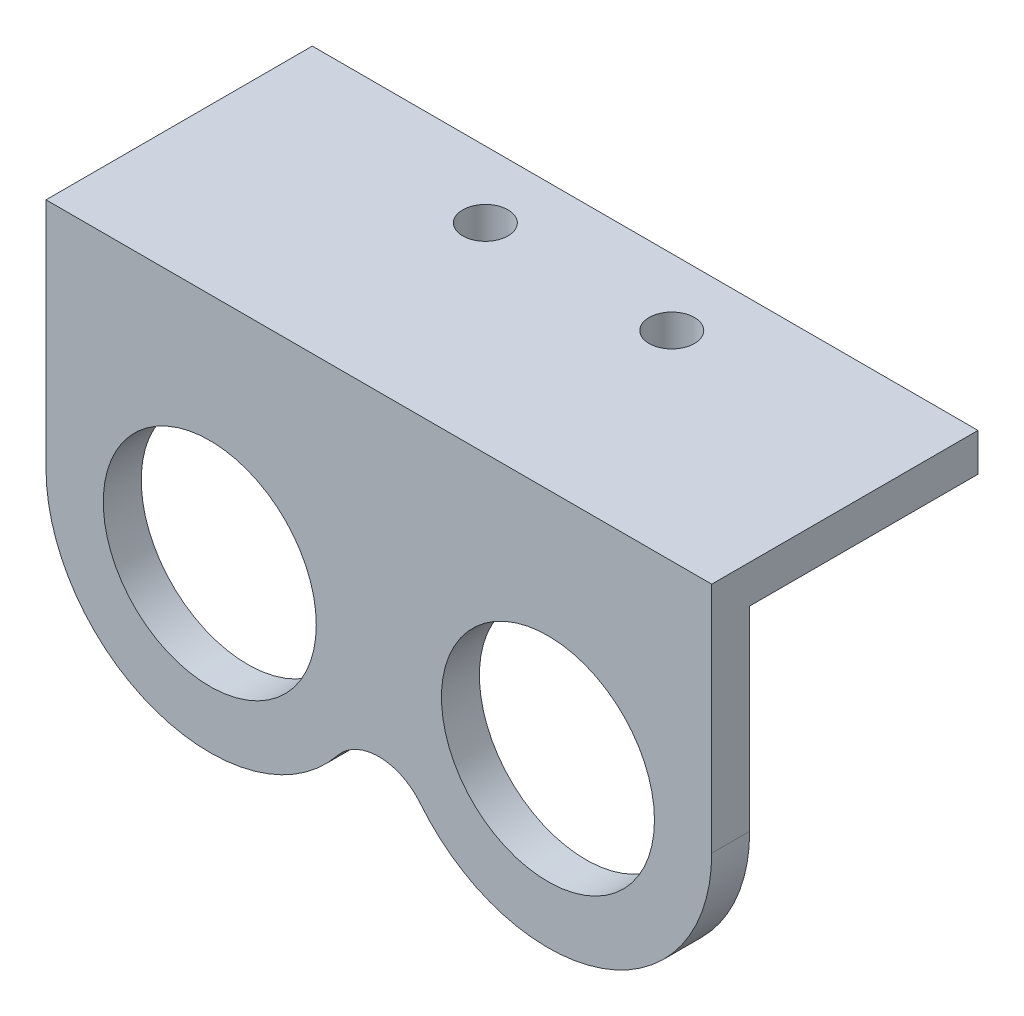
SolidWorks part; units mm, degrees
ref_plane "Front Plane" through (0, 0, 0) normal (0, 0, 1) x (1, 0, 0)
ref_plane "Top Plane" through (0, 0, 0) normal (0, 1, 0) x (1, 0, 0)
ref_plane "Right Plane" through (0, 0, 0) normal (1, 0, 0) x (0, 0, -1)
sketch "Sketch2" plane through (0, 0, 0) normal (0, 0, 1) x (1, 0, 0)
  line L0 (-12.7, 0) -> (12.7, 0) construction
  line L1 (-25, 17.5) -> (-25, 0)
  line L2 (25, 0) -> (25, 17.5)
  line L3 (25, 17.5) -> (-25, 17.5)
  circle A0 centre (12.7, 0) radius 8
  circle A1 centre (-12.7, 0) radius 8
  arc A2 (-25, 0) -> (-3.1166, -7.7102) centre (-12.7, 0) ccw
  arc A3 (-3.1166, -7.7102) -> (3.1166, -7.7102) centre (0, -10.2176) cw
  arc A4 (3.1166, -7.7102) -> (25, 0) centre (12.7, 0) ccw
  point P4 (0, 0)
  dimension "D1" = 16
  dimension "D4" = 4
  dimension "D2" = 25.4
  dimension "D3" = 50
  dimension "D5" = 17.5
extrude "Boss-Extrude1" add sketch "Sketch2" along normal blind 2.85
sketch "Sketch3" plane through (-25, 0, 0) normal (-1, 0, 0) x (0, 0, 1)
  line L0 (2.85, 17.5) -> (0, 17.5) construction
  line L1 (0, 17.5) -> (-17.15, 17.5)
  line L2 (0, 17.5) -> (0, 14.65)
  line L3 (0, 14.65) -> (-17.15, 14.65)
  line L4 (-17.15, 17.5) -> (-17.15, 14.65)
  line L5 (2.85, 17.5) -> (2.85, 0) construction
  dimension "D1" = 20
extrude "Boss-Extrude2" add sketch "Sketch3" against normal up to surface (50 mm away) up to face at (25, 8.75, 1.425)
sketch "Sketch4" plane through (0, 17.5, 0) normal (0, 1, 0) x (1, 0, 0)
  line L0 (-7, 12.15) -> (7, 12.15) construction
  line L1 (25, 17.15) -> (-25, 17.15) construction
  circle A0 centre (-7, 12.15) radius 1.7
  circle A1 centre (7, 12.15) radius 1.7
  point P2 (0, 12.15)
  dimension "D1" = 3.4
  dimension "D2" = 14
  dimension "D3" = 5
extrude "Cut-Extrude1" cut sketch "Sketch4" against normal up to surface (2.85 mm away) up to face at (0, 14.65, -8.575)
